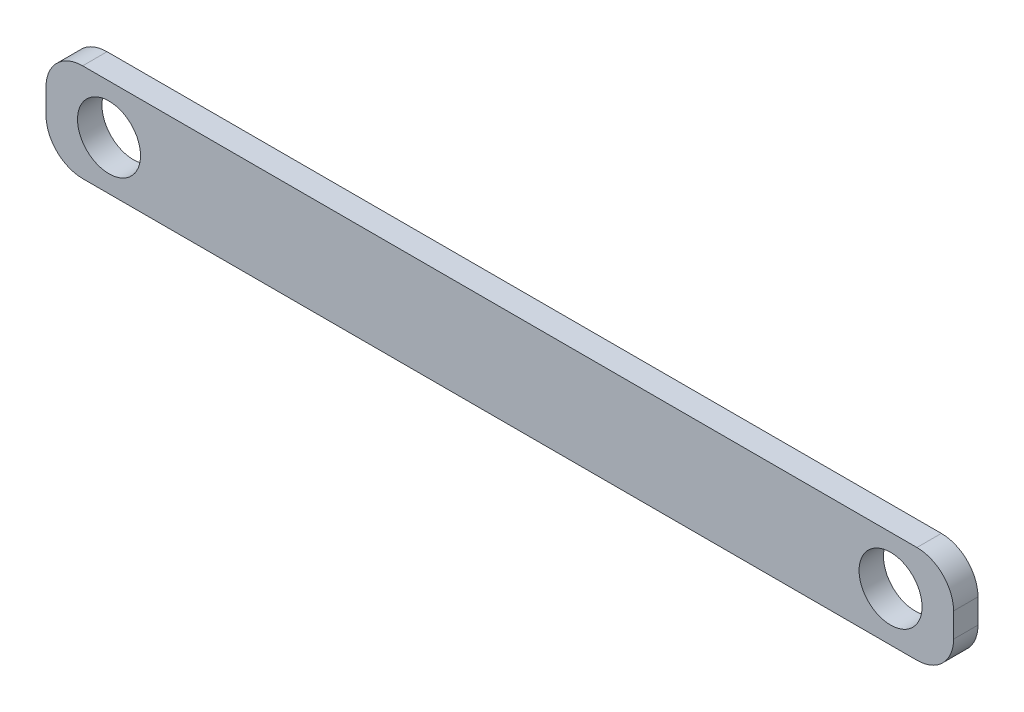
SolidWorks part; units mm, degrees
material "Teak"
ref_plane "Front Plane" through (0, 0, 0) normal (0, 0, 1) x (1, 0, 0)
ref_plane "Top Plane" through (0, 0, 0) normal (0, 1, 0) x (1, 0, 0)
ref_plane "Right Plane" through (0, 0, 0) normal (1, 0, 0) x (0, 0, -1)
sketch "Sketch1" plane through (0, 0, 0) normal (0, 0, 1) x (1, 0, 0)
  line L0 (-92.9, -10) -> (92.9, -10)
  line L1 (-92.9, -10) -> (-92.9, 10)
  line L2 (92.9, -10) -> (92.9, 10)
  line L3 (-92.9, 10) -> (92.9, 10)
  line L4 (-92.9, -10) -> (92.9, 10) construction
  line L5 (92.9, -10) -> (-92.9, 10) construction
  line L6 (-92.9, 0) -> (92.9, 0) construction
  line L7 (0, 10) -> (0, -10) construction
  circle A0 centre (-80, 0) radius 6.45
  circle A1 centre (80, 0) radius 6.45
  point P1 (0, 0)
  dimension "D3" = 12.9
  dimension "D1" = 160
  dimension "D2" = 20
  dimension "D4" = 12.9
extrude "Boss-Extrude1" add sketch "Sketch1" along normal blind 5
fillet "Fillet1" radius 7.5 4 edges at (-92.9, -10, 2.5) (-92.9, 10, 2.5) (92.9, -10, 2.5) (92.9, 10, 2.5)
equation "\"D1@Boss-Extrude1\"=5mm"
equation "\"p\"= 20mm"
equation "\"m\"= 1"
equation "\"hole_diam\"= 4mm"
equation "\"len_grip_1\" = 50mm"
equation "\"len_grip_2\" = 50mm"
equation "\"thick\" = 3.1mm"
equation "\"thick2\" = 20mm"
equation "\"wrist_cont_bearing_diam\"=3in"
equation "\"wrist_cont_bearing_thick\"=5/16in"
equation "\"len_forearm\" = 300mm"
equation "\"wrist_bearing_diam\"=3in"
equation "\"len_link\" = 7cm"
equation "\"D4@Sketch1\"=\"D3@Sketch1\""
